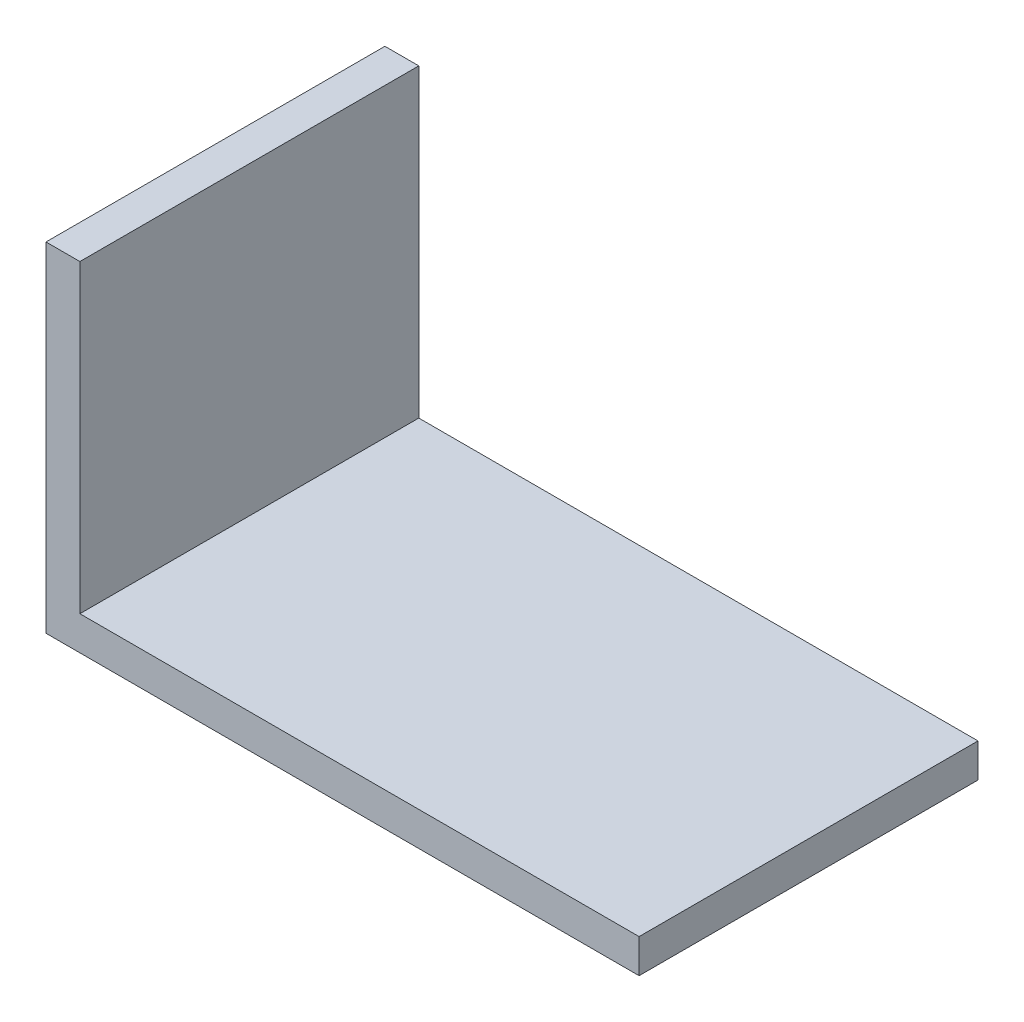
SolidWorks part; units mm, degrees
material "1060 Сплав"
ref_plane "Спереди" through (0, 0, 0) normal (0, 0, 1) x (1, 0, 0)
ref_plane "Сверху" through (0, 0, 0) normal (0, 1, 0) x (1, 0, 0)
ref_plane "Справа" through (0, 0, 0) normal (1, 0, 0) x (0, 0, -1)
sketch "Эскиз1" plane through (0, 0, 0) normal (0, 0, 1) x (1, 0, 0)
  line L0 (0, 0) -> (35, 0)
  line L1 (35, 0) -> (35, 2)
  line L2 (35, 2) -> (2, 2)
  line L3 (2, 2) -> (2, 20)
  line L4 (2, 20) -> (0, 20)
  line L5 (0, 20) -> (0, 0)
  dimension "D1" = 35
  dimension "D2" = 2
  dimension "D3" = 20
extrude "Бобышка-Вытянуть1" add sketch "Эскиз1" along normal blind 20
